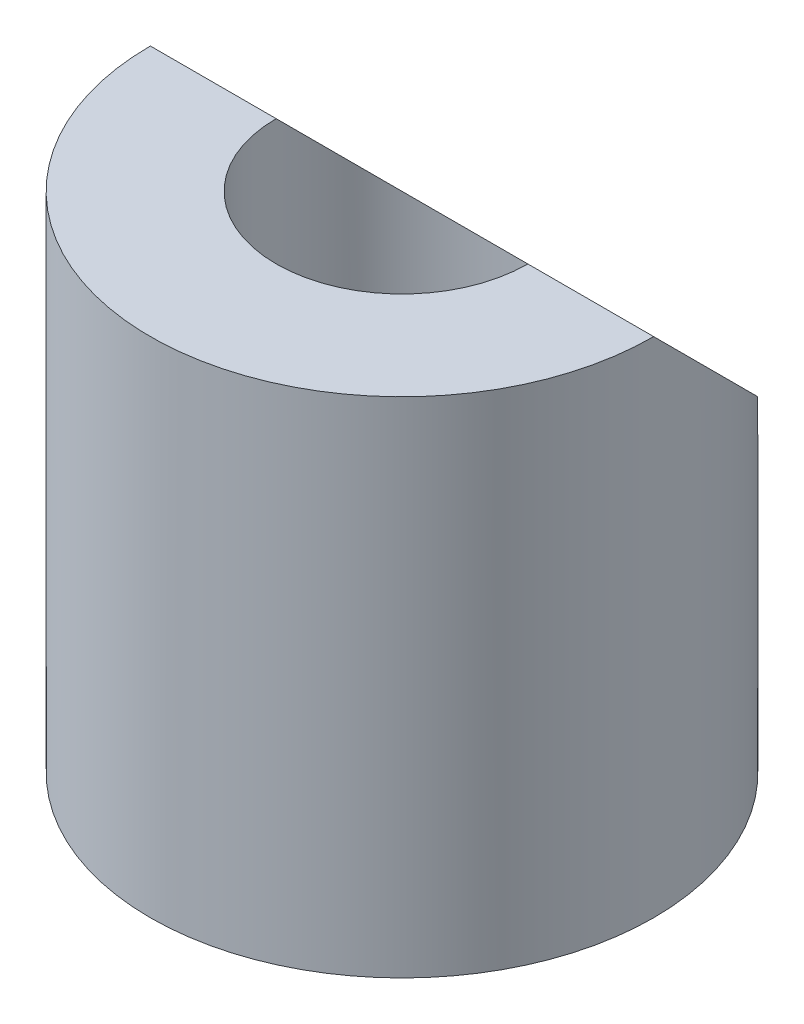
SolidWorks part; units mm, degrees
ref_plane "Front" through (0, 0, 0) normal (0, 0, 1) x (1, 0, 0)
ref_plane "Top" through (0, 0, 0) normal (0, 1, 0) x (1, 0, 0)
ref_plane "Right" through (0, 0, 0) normal (1, 0, 0) x (0, 0, -1)
sketch "Sketch1" plane through (0, 0, 0) normal (0, 1, 0) x (1, 0, 0)
  circle A0 centre (0, 0) radius 2
  circle A1 centre (0, 0) radius 1
  dimension "D1" = 4
  dimension "D2" = 2
extrude "Boss-Extrude1" add sketch "Sketch1" along normal blind 4
sketch "Sketch2" plane through (0, 0, 0) normal (1, 0, 0) x (0, 0, -1)
  line L2 (2, 4) -> (-2, 4) construction
  line L3 (0, 4) -> (2, 2)
  line L4 (2, 0) -> (2, 4) construction
  line L5 (2, 2) -> (2, 4)
  line L6 (2, 4) -> (0, 4)
extrude "Cut-Extrude1" cut sketch "Sketch2" against normal mid plane 4
